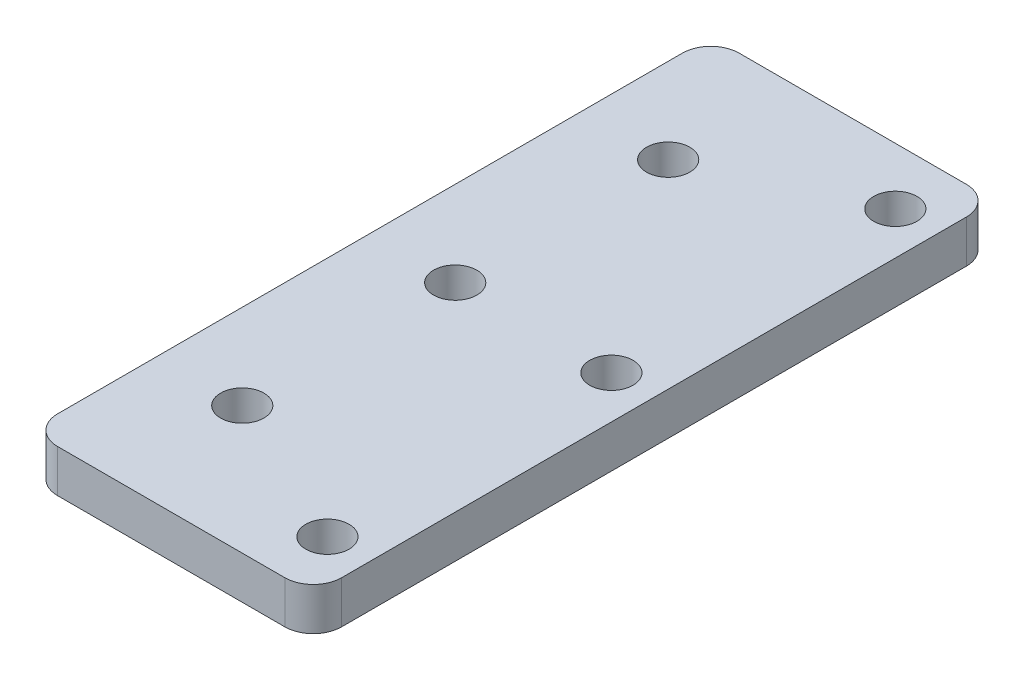
SolidWorks part; units mm, degrees
material "Thornel Mat VMA"
ref_plane "前视基准面" through (0, 0, 0) normal (0, 0, 1) x (1, 0, 0)
ref_plane "上视基准面" through (0, 0, 0) normal (0, 1, 0) x (1, 0, 0)
ref_plane "右视基准面" through (0, 0, 0) normal (1, 0, 0) x (0, 0, -1)
other "Configuration Table"
sketch "草图1" plane through (0, 0, 0) normal (0, 1, 0) x (1, 0, 0)
  line L1 (-10, -24) -> (10, -24)
  line L2 (-10, -24) -> (-10, 24)
  line L3 (-10, 24) -> (10, 24)
  line L4 (10, -24) -> (10, 24)
  line L5 (-10, -24) -> (10, 24) construction
  line L6 (-10, 24) -> (10, -24) construction
  point P0 (0, 0)
  dimension "D1" = 20
  dimension "D2" = 48
extrude "凸台-拉伸1" add sketch "草图1" along normal blind 3
sketch "草图2" plane through (0, 3, 0) normal (0, 1, 0) x (1, 0, 0)
  line L0 (7, 24) -> (7, 50024) construction
  line L1 (-4, 0) -> (-4, 50000) construction
  line L2 (10, -24) -> (10, 24) construction
  line L3 (0, 0) -> (50000, 0) construction
  circle A0 centre (7, 0) radius 1.525
  circle A1 centre (7, 20) radius 1.525
  circle A2 centre (-4, 0) radius 1.525
  circle A3 centre (-4, 15) radius 1.525
  circle A4 centre (7, -20) radius 1.525
  circle A5 centre (-4, -15) radius 1.525
  dimension "D2" = 3.05
  dimension "D3" = 20
  dimension "D1" = 3
  dimension "D4" = 11
  dimension "D5" = 15
extrude "切除-拉伸1" cut sketch "草图2" against normal through all
fillet "圆角1" radius 2 4 edges at (-10, 1.5, -24) (10, 1.5, 24) (-10, 1.5, 24) (10, 1.5, -24)
